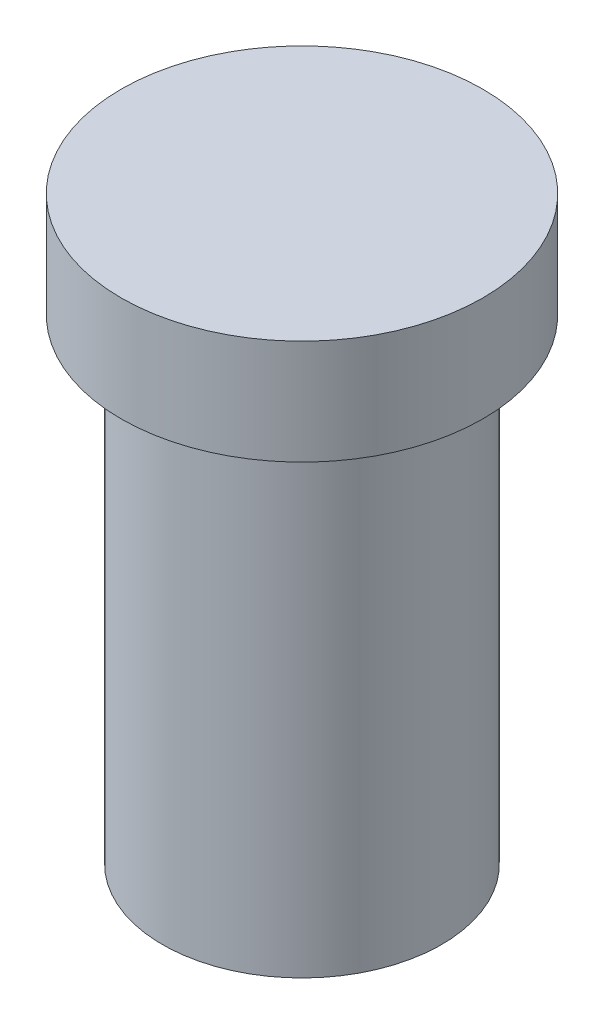
SolidWorks part; units mm, degrees
ref_plane "Front Plane" through (0, 0, 0) normal (0, 0, 1) x (1, 0, 0)
ref_plane "Top Plane" through (0, 0, 0) normal (0, 1, 0) x (1, 0, 0)
ref_plane "Right Plane" through (0, 0, 0) normal (1, 0, 0) x (0, 0, -1)
sketch "Sketch1" plane through (0, 0, 0) normal (0, 0, 1) x (1, 0, 0)
  line L0 (0, 0) -> (0, 96.6253) construction
  line L1 (0, 0) -> (22, 0)
  line L2 (22, 0) -> (22, 75)
  line L3 (22, 75) -> (28.5, 75)
  line L4 (28.5, 75) -> (28.5, 91.5109)
  line L5 (28.5, 91.5109) -> (0, 91.5109)
  line L6 (0, 0) -> (0, 91.5109)
  point P10 (0, 91.5109)
  dimension "D3" = 75
revolve "Revolve3" add sketch "Sketch1" angle 360 about L0
fillet "Fillet1" radius 3 1 edges at (0, 75, -22)
